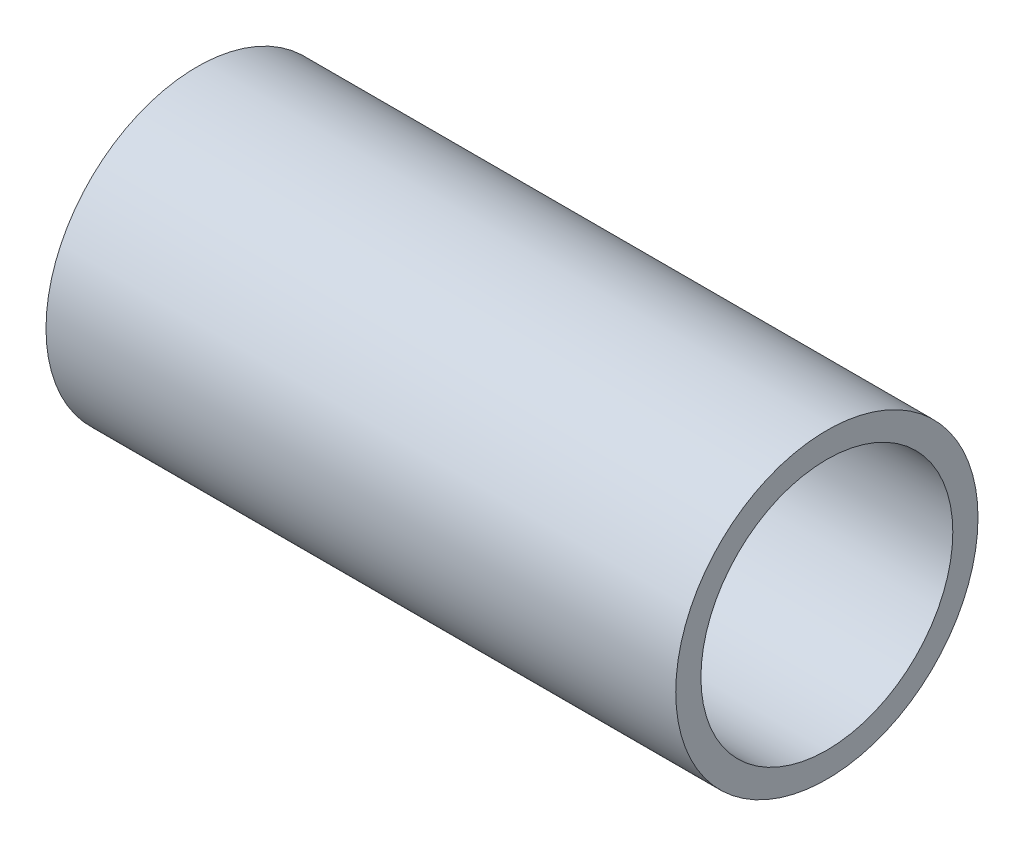
SolidWorks part; units mm, degrees
ref_plane "Ebene vorne" through (0, 0, 0) normal (0, 0, 1) x (1, 0, 0)
ref_plane "Ebene oben" through (0, 0, 0) normal (0, 1, 0) x (1, 0, 0)
ref_plane "Ebene rechts" through (0, 0, 0) normal (1, 0, 0) x (0, 0, -1)
sketch "Skizze1" plane through (0, 0, 0) normal (0, 1, 0) x (1, 0, 0)
  line L0 (0, 0) -> (0, 6)
  line L1 (0, 6) -> (25, 6)
  line L2 (25, 6) -> (25, 5)
  line L3 (25, 5) -> (0, 5)
  line L4 (0, 0) -> (25, 0) construction
revolve "Rotation1" add sketch "Skizze1" angle 360 about L4
